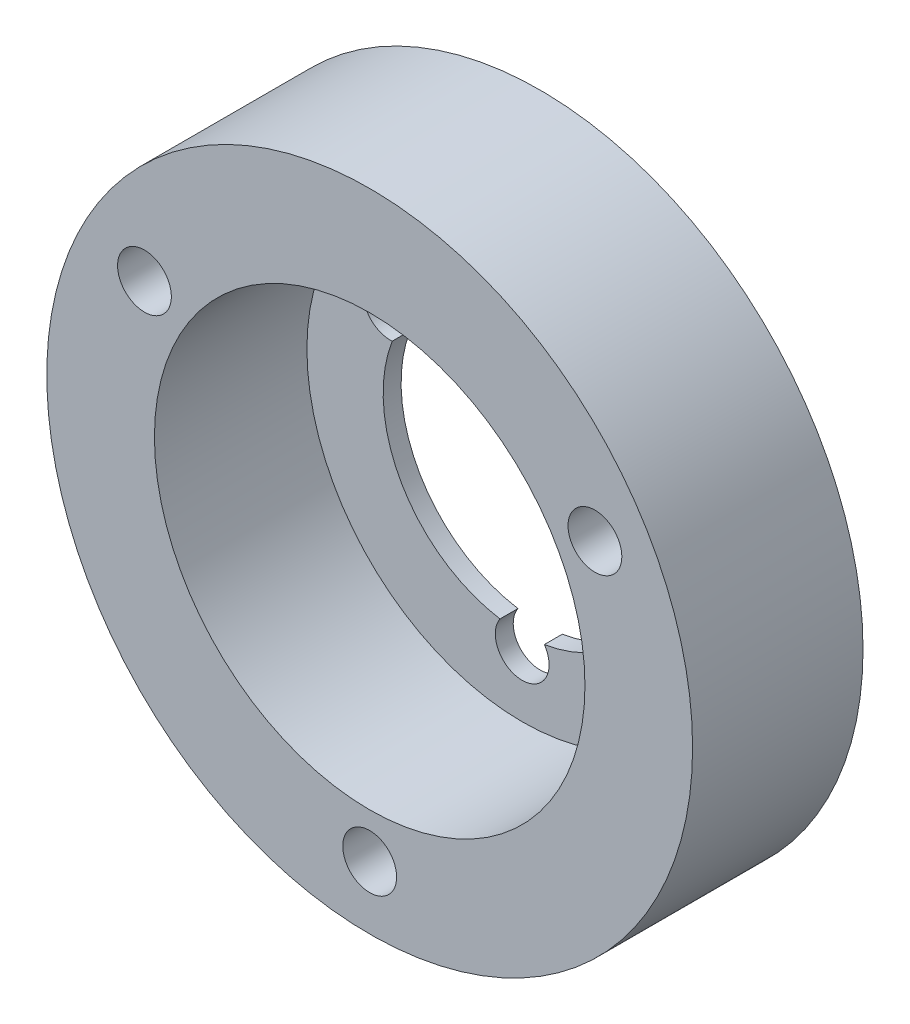
SolidWorks part; units mm, degrees
ref_plane "Plan de face" through (0, 0, 0) normal (0, 0, 1) x (1, 0, 0)
ref_plane "Plan de dessus" through (0, 0, 0) normal (0, 1, 0) x (1, 0, 0)
ref_plane "Plan de droite" through (0, 0, 0) normal (1, 0, 0) x (0, 0, -1)
sketch "Esquisse1" plane through (0, 0, 0) normal (0, 1, 0) x (1, 0, 0)
  line L0 (0, 0) -> (50, 0)
  line L1 (50, 0) -> (50, -9.5)
  line L2 (50, -9.5) -> (0, -9.5)
  line L3 (0, 0) -> (0, -9.5)
extrude "Extrusion1" add sketch "Esquisse1" along normal blind 45
sketch "Esquisse2" plane through (0, 0, 9.5) normal (0, 0, 1) x (1, 0, 0)
  circle A1 centre (12.445, 29.7486) radius 1.5
  circle A2 centre (37.555, 29.7486) radius 1.5
  circle A3 centre (25, 8.0027) radius 1.5
  arc A13 (17.7561, 25.2546) -> (18.9925, 27.3961) centre (17.6388, 26.75) cw
  arc A14 (18.9925, 27.3961) -> (31.0075, 27.3961) centre (25, 22.5) cw
  arc A15 (31.0075, 27.3961) -> (32.2439, 25.2546) centre (32.3612, 26.75) cw
  arc A16 (32.2439, 25.2546) -> (26.2364, 14.8493) centre (25, 22.5) cw
  arc A17 (26.2364, 14.8493) -> (23.7636, 14.8493) centre (25, 14) cw
  arc A18 (23.7636, 14.8493) -> (17.7561, 25.2546) centre (25, 22.5) cw
extrude "Extrusion2" cut sketch "Esquisse2" against normal blind 45
sketch "Esquisse3" plane through (0, 0, 9.5) normal (0, 0, 1) x (1, 0, 0)
  circle A0 centre (25, 22.5) radius 12
extrude "Extrusion3" cut sketch "Esquisse3" against normal blind 8.5
sketch "Esquisse4" plane through (0, 0, 9.5) normal (0, 0, 1) x (1, 0, 0)
  circle A0 centre (25, 22.5) radius 18
  circle A1 centre (25, 22.5) radius 36.1203
extrude "Extrusion4" cut sketch "Esquisse4" against normal through all
